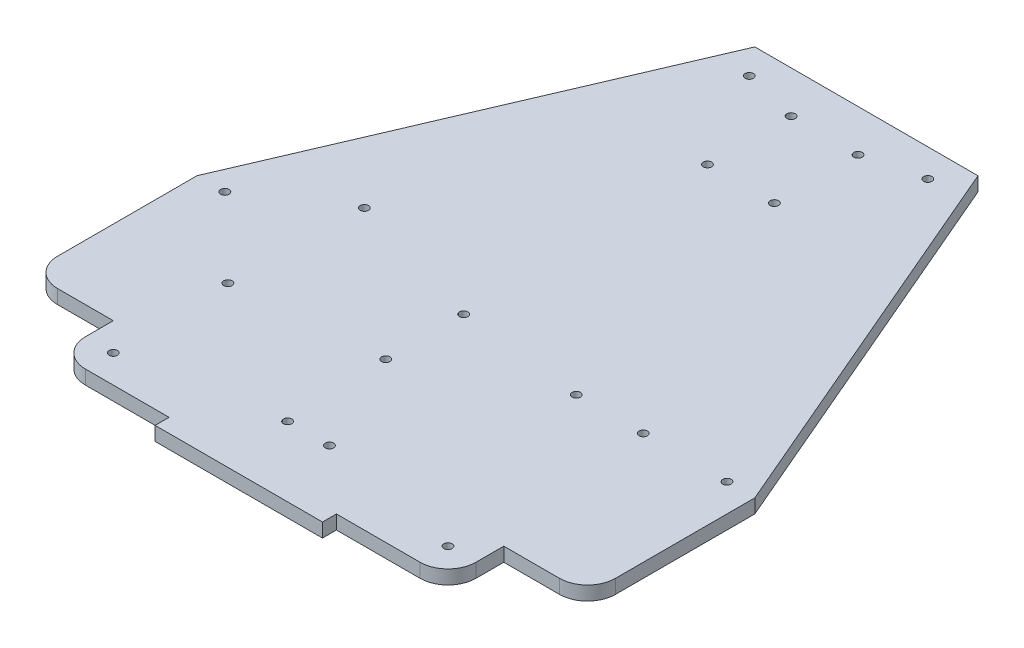
SolidWorks part; units mm, degrees
ref_plane "Front Plane" through (0, 0, 0) normal (0, 0, 1) x (1, 0, 0)
ref_plane "Top Plane" through (0, 0, 0) normal (0, 1, 0) x (1, 0, 0)
ref_plane "Right Plane" through (0, 0, 0) normal (1, 0, 0) x (0, 0, -1)
sketch "Sketch1" plane through (0, 0, 0) normal (0, 1, 0) x (1, 0, 0)
  line L8 (100, -40) -> (100, 10)
  line L10 (-40, 150) -> (40, 150)
  line L11 (40, 150) -> (100, 10)
  line L12 (-40, 150) -> (-100, 10)
  line L13 (-100, -40) -> (-100, 10)
  line L17 (70, -60) -> (70, -50)
  line L18 (70, -50) -> (90, -50)
  line L19 (-70, -60) -> (-70, -50)
  line L20 (-70, -50) -> (-90, -50)
  line L26 (-60, -70) -> (-30, -70)
  line L27 (-30, -70) -> (-30, -75)
  line L28 (-30, -75) -> (30, -75)
  line L29 (30, -75) -> (30, -70)
  line L30 (30, -70) -> (60, -70)
  arc A4 (-70, -60) -> (-60, -70) centre (-60, -60) ccw
  arc A5 (60, -70) -> (70, -60) centre (60, -60) ccw
  arc A6 (90, -50) -> (100, -40) centre (90, -40) ccw
  arc A7 (-90, -50) -> (-100, -40) centre (-90, -40) cw
  point P9 (-70, -70)
  point P15 (100, -70)
  point P16 (70, -70)
  point P21 (0, -70)
  point P24 (-100, -70)
  dimension "D6" = 5
  dimension "D3" = 10
  dimension "D1" = 80
  dimension "D2" = 200
  dimension "D4" = 30
  dimension "D5" = 30
  dimension "D7" = 20
  dimension "D8" = 20
  dimension "D9" = 60
  dimension "D10" = 60
  dimension "D11" = 5
extrude "Boss-Extrude1" add sketch "Sketch1" along normal blind 5
sketch "Sketch3" plane through (0, 5, 0) normal (0, 1, 0) x (1, 0, 0)
  line L0 (-100, 30) -> (-60, 30) construction
  line L1 (-60, 30) -> (-9.2, 30) construction
  line L2 (-9.2, 30) -> (-9.2, 14.8) construction
  line L3 (-9.2, 14.8) -> (-9.2, -13.1) construction
  line L4 (-9.2, -13.1) -> (-9.2, -17.8) construction
  line L5 (-9.2, -17.8) -> (-61.1, -17.8) construction
  line L6 (-61.1, -17.8) -> (-60, -17.8) construction
  line L7 (-60, -17.8) -> (-60, 30) construction
  line L8 (-100, 10) -> (-100, 30) construction
  circle A0 centre (-61.1, -17.8) radius 1.5
  circle A1 centre (-9.2, -13.1) radius 1.5
  circle A2 centre (-9.2, 14.8) radius 1.5
  circle A3 centre (-60, 30) radius 1.5
  dimension "D8" = 3
  dimension "D9" = 3
  dimension "D10" = 3
  dimension "D11" = 3
  dimension "D1" = 40
  dimension "D2" = 50.8
  dimension "D3" = 15.2
  dimension "D4" = 27.9
  dimension "D5" = 4.7
  dimension "D6" = 51.9
  dimension "D7" = 1.1
  dimension "D12" = 20
extrude "Cut-Extrude2" cut sketch "Sketch3" against normal through all
sketch "Sketch6" plane through (0, 5, 0) normal (0, 1, 0) x (1, 0, 0)
  line L0 (0, 150) -> (0, 120) construction
  line L2 (40, 150) -> (-40, 150) construction
  line L3 (-12, 135) -> (12, 135) construction
  line L4 (-12, 135) -> (-12, 105) construction
  line L5 (-12, 105) -> (12, 105) construction
  line L6 (12, 135) -> (12, 105) construction
  line L7 (-12, 135) -> (12, 105) construction
  line L8 (-12, 105) -> (12, 135) construction
  circle A0 centre (12, 135) radius 1.5
  circle A1 centre (-12, 135) radius 1.5
  circle A2 centre (12, 105) radius 1.5
  circle A3 centre (-12, 105) radius 1.5
  dimension "D4" = 3
  dimension "D5" = 3
  dimension "D6" = 3
  dimension "D7" = 3
  dimension "D1" = 30
  dimension "D2" = 30
  dimension "D3" = 24
extrude "Cut-Extrude4" cut sketch "Sketch6" against normal through all
sketch "Sketch8" plane through (0, 5, 0) normal (0, 1, 0) x (1, 0, 0)
  line L0 (-70, -60) -> (-60, -60) construction
  line L1 (0, -75) -> (0, -50) construction
  line L2 (-40, 150) -> (-32, 150) construction
  line L3 (40, 150) -> (-40, 150) construction
  line L4 (-32, 150) -> (-32, 140) construction
  line L5 (-30, -75) -> (30, -75) construction
  line L6 (0, 150) -> (0, 38.0278) construction
  line L7 (0, -50) -> (-7.5, -50) construction
  circle A2 centre (-90, 10) radius 1.5
  circle A3 centre (-32, 140) radius 1.5
  circle A6 centre (90, 10) radius 1.5
  circle A7 centre (32, 140) radius 1.5
  circle A8 centre (-60, -60) radius 1.5
  circle A9 centre (60, -60) radius 1.5
  circle A10 centre (-7.5, -50) radius 1.5
  circle A11 centre (7.5, -50) radius 1.5
  dimension "D6" = 7.5
  dimension "D7" = 3
  dimension "D8" = 3
  dimension "D9" = 3
  dimension "D2" = 3
  dimension "D1" = 10
  dimension "D3" = 8
  dimension "D4" = 10
  dimension "D5" = 25
extrude "Cut-Extrude5" cut sketch "Sketch8" against normal blind 10
sketch "Sketch9" plane through (0, 5, 0) normal (0, 1, 0) x (1, 0, 0)
  line L0 (100, 10) -> (60, 10) construction
  line L1 (60, 10) -> (36, 10) construction
  circle A0 centre (60, 10) radius 1.5
  circle A1 centre (36, 10) radius 1.5
  dimension "D3" = 3
  dimension "D4" = 3
  dimension "D1" = 40
  dimension "D2" = 24
extrude "Cut-Extrude6" cut sketch "Sketch9" against normal blind 10
